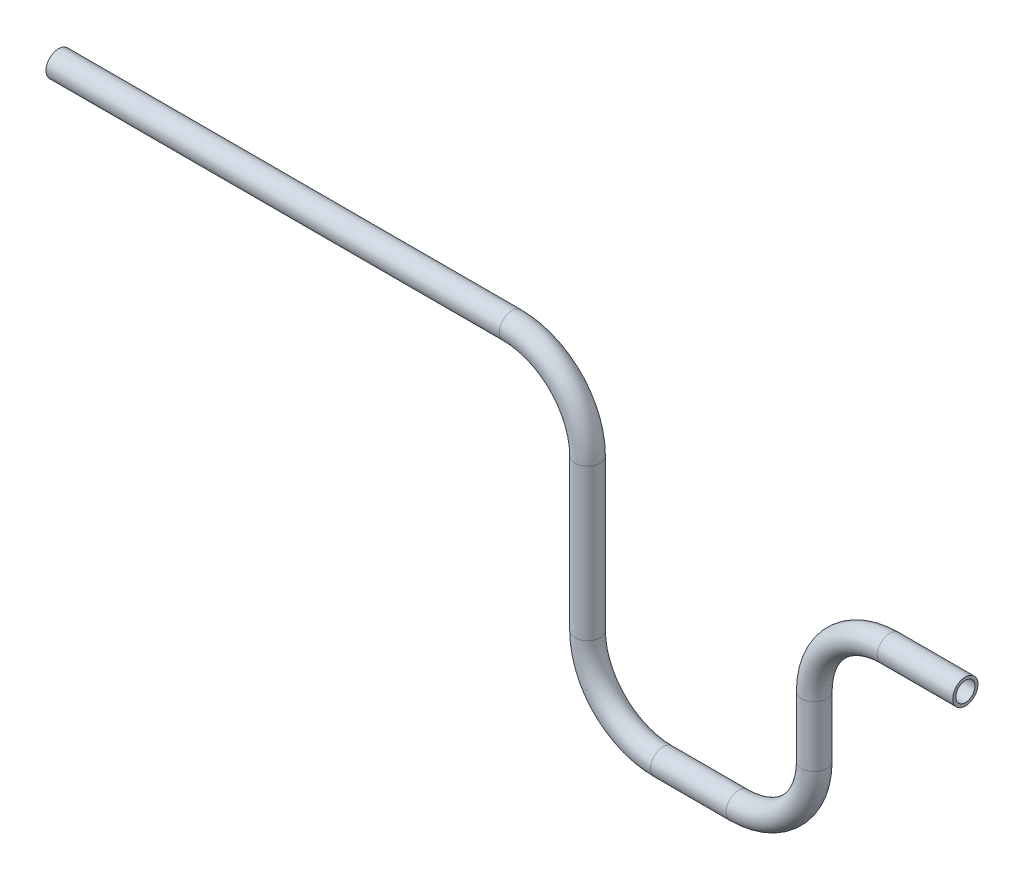
SolidWorks part; units mm, degrees
ref_plane "Alzado" through (0, 0, 0) normal (0, 0, 1) x (1, 0, 0)
ref_plane "Planta" through (0, 0, 0) normal (0, 1, 0) x (1, 0, 0)
ref_plane "Vista lateral" through (0, 0, 0) normal (1, 0, 0) x (0, 0, -1)
sketch "Croquis1" plane through (0, 0, 0) normal (0, 0, 1) x (1, 0, 0)
  line L0 (0, 0) -> (300, 0)
  line L1 (350, -50) -> (350, -150)
  line L2 (400, -200) -> (450, -200)
  line L3 (500, -150) -> (500, -110)
  line L4 (550, -60) -> (600, -60)
  arc A0 (300, 0) -> (350, -50) centre (300, -50) cw
  arc A1 (350, -150) -> (400, -200) centre (400, -150) ccw
  arc A2 (450, -200) -> (500, -150) centre (450, -150) ccw
  arc A3 (500, -110) -> (550, -60) centre (550, -110) cw
  dimension "D4" = 50
  dimension "D1" = 200
  dimension "D2" = 300
  dimension "D3" = 40
  dimension "D5" = 50
  dimension "D6" = 50
sketch "Croquis2" plane through (0, 0, 0) normal (1, 0, 0) x (0, 0, -1)
  circle A0 centre (0, 0) radius 8.35
  dimension "D1" = 16.7
sweep "Barrer1" add profiles "Croquis2" path "Croquis1"
shell "Vaciado1" thickness 2
